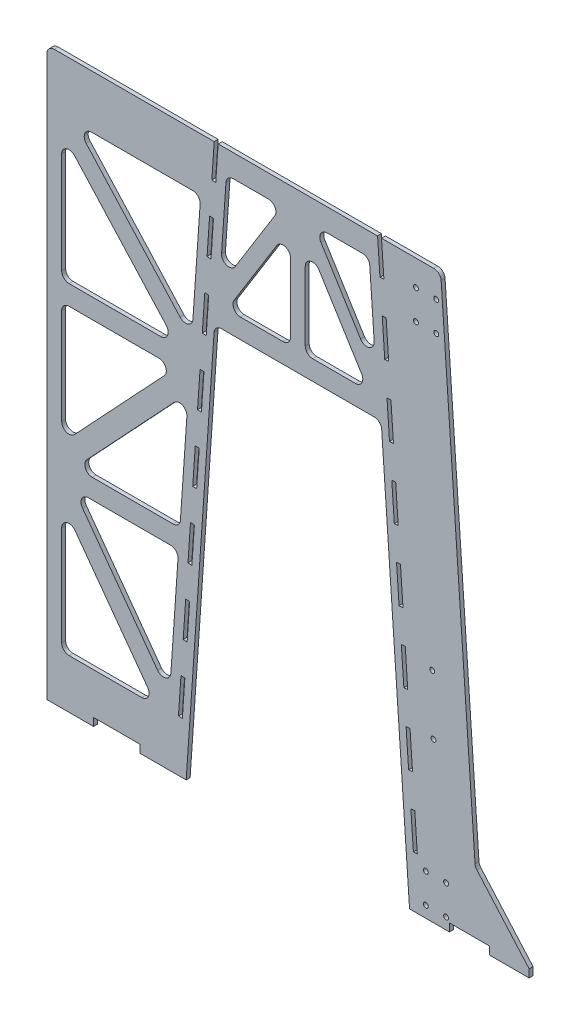
SolidWorks part; units mm, degrees
material "A-Glass Fiber"
ref_plane "Front Plane" through (0, 0, 0) normal (0, 0, 1) x (1, 0, 0)
ref_plane "Top Plane" through (0, 0, 0) normal (0, 1, 0) x (1, 0, 0)
ref_plane "Right Plane" through (0, 0, 0) normal (1, 0, 0) x (0, 0, -1)
sketch "Sketch1" plane through (0, 0, 0) normal (0, 0, 1) x (1, 0, 0)
  line L0 (-288.2759, 0) -> (288.2759, 0) construction
  line L1 (-215.8925, 1463.04) -> (215.8925, 1463.04)
  line L2 (0, 0) -> (0, 1733.4513) construction
  line L3 (19.05, 1104.9) -> (205.1391, 1104.9)
  line L4 (202.3135, 1145.5664) -> (41.4731, 1404.62)
  line L5 (205.1391, 1104.9) -> (19.05, 1404.62) construction
  line L6 (205.1391, 1104.9) -> (184.3133, 1404.62)
  line L7 (182.716, 1104.9) -> (19.05, 1368.5047)
  line L8 (19.05, 1404.62) -> (19.05, 1104.9)
  line L9 (184.3133, 1404.62) -> (19.05, 1404.62)
  line L10 (205.7153, 1463.04) -> (307.3735, 0)
  line L11 (317.5154, 0.5076) -> (215.8925, 1463.04)
  line L12 (317.5154, 0.5076) -> (317.5507, 0)
  line L13 (288.2759, 0) -> (215.0326, 1054.1)
  line L14 (494.0591, 0) -> (391.1675, 0) construction
  line L15 (266.6925, 1463.04) -> (368.5375, 1463.04)
  line L16 (368.5375, 1463.04) -> (457.7693, 178.8376)
  line L81 (215.8925, 1463.04) -> (266.6925, 1463.04)
  line L82 (-215.8925, 1463.04) -> (-647.7182, 1463.04)
  line L88 (317.5507, 0) -> (307.3718, 0)
  line L90 (215.0326, 1054.1) -> (-215.0326, 1054.1)
  line L92 (307.3718, 0) -> (288.2759, 0)
  line L93 (-288.2759, 0) -> (-215.0326, 1054.1)
  line L94 (-307.3735, 0) -> (-288.2759, 0)
  line L97 (-317.5507, 0) -> (-307.3735, 0)
  line L98 (-317.5154, 0.5076) -> (-317.5507, 0)
  line L99 (-317.5154, 0.5076) -> (-215.8925, 1463.04)
  line L100 (-205.7153, 1463.04) -> (-307.3735, 0)
  line L124 (-184.3133, 1404.62) -> (-19.05, 1404.62)
  line L125 (-19.05, 1404.62) -> (-19.05, 1104.9)
  line L126 (-182.716, 1104.9) -> (-19.05, 1368.5047)
  line L127 (-205.1391, 1104.9) -> (-19.05, 1404.62) construction
  line L128 (-202.3135, 1145.5664) -> (-41.4731, 1404.62)
  line L129 (-205.1391, 1104.9) -> (-184.3133, 1404.62)
  line L130 (-19.05, 1104.9) -> (-205.1391, 1104.9)
  line L131 (-317.5507, 0) -> (-647.7182, 0)
  line L132 (-647.7182, 0) -> (-647.7182, 1463.04)
  line L133 (-647.7182, 0) -> (-317.5507, 0)
  line L134 (-308.7262, 127) -> (-647.7182, 127)
  line L135 (-647.7182, 1325.88) -> (-225.423, 1325.88)
  line L136 (317.5507, 0) -> (368.3507, 0)
  line L137 (368.3507, 0) -> (266.6925, 1463.04)
  line L138 (368.3507, 0) -> (317.5507, 0)
  line L139 (-250.8842, 1325.88) -> (-334.1875, 127)
  line L140 (-609.6182, 127) -> (-609.6182, 1325.88)
  line L141 (-306.1844, 530.0133) -> (-609.6182, 530.0133)
  line L142 (-278.1813, 933.0267) -> (-609.6182, 933.0267)
  line L143 (-304.4195, 555.4133) -> (-609.6182, 555.4133)
  line L144 (-307.9493, 504.6133) -> (-609.6182, 504.6133)
  line L145 (-279.9462, 907.6267) -> (-609.6182, 907.6267)
  line L146 (-276.4164, 958.4267) -> (-609.6182, 958.4267)
  line L147 (-334.1875, 127) -> (-609.6182, 504.6133) construction
  line L148 (-609.6182, 555.4133) -> (-279.9462, 907.6267) construction
  line L149 (-276.4164, 958.4267) -> (-609.6182, 1325.88) construction
  line L150 (-331.453, 166.3535) -> (-578.1794, 504.6133)
  line L151 (-574.8276, 555.4133) -> (-282.736, 867.4768)
  line L152 (-273.976, 993.5478) -> (-575.3304, 1325.88)
  line L153 (-365.6263, 127) -> (-609.6182, 461.511)
  line L154 (-609.6182, 592.5827) -> (-314.7368, 907.6267)
  line L155 (-310.7042, 958.4267) -> (-609.6182, 1288.0676)
  line L156 (368.3507, 0) -> (596.9507, 0)
  line L157 (596.9507, 0) -> (596.9507, 20.32)
  line L158 (596.9507, 20.32) -> (347.1719, 304.8)
  point P0 (0, 0)
  point P3 (0, 0)
  point P106 (0, 0)
  point P118 (0, 1054.1)
  dimension "D6" = 25.4
  dimension "D7" = 50.8
  dimension "D8" = 58.42
  dimension "D9" = 19.05
  dimension "D10" = 647.7182
  dimension "D11" = 10.1527
  dimension "D12" = 25.4
  dimension "D13" = 25.4
  dimension "D14" = 25.4
  dimension "D15" = 25.4
  dimension "D16" = 25.4
  dimension "D17" = 25.4
  dimension "D18" = 1463.04
  dimension "D19" = 288.2759
  dimension "D20" = 29.2044
  dimension "D21" = 101.6
  dimension "D22" = 19.05
  dimension "D23" = 19.05
  dimension "D24" = 1054.1
  dimension "D25" = 20.32
  dimension "D37" = 127
  dimension "D38" = 50.8
  dimension "D39" = 25.4
  dimension "D40" = 38.1
  dimension "D41" = 403.0133
  dimension "D42" = 403.0133
  dimension "D43" = 25.4
  dimension "D44" = 25.4
  dimension "D45" = 25.4
  dimension "D46" = 25.4
  dimension "D47" = 279.4
  dimension "D48" = 304.8
  dimension "D49" = 50.8
  dimension "D52" = 137.16
extrude "Boss-Extrude1" add sketch "Sketch1" along normal blind 10.16
fillet "Fillet1" radius 19.05 35 edges at (-215.0326, 1054.1, 5.08) (215.0326, 1054.1, 5.08) (-202.3135, 1145.5664, 5.08) (-19.05, 1104.9, 5.08) (-182.716, 1104.9, 5.08) (-19.05, 1368.5047, 5.08) (-41.4731, 1404.62, 5.08) (-184.3133, 1404.62, 5.08) (-647.7182, 1463.04, 5.08) (-250.8842, 1325.88, 5.08) (-575.3304, 1325.88, 5.08) (-273.976, 993.5478, 5.08) (-609.6182, 958.4267, 5.08) (-609.6182, 1288.0676, 5.08) (-310.7042, 958.4267, 5.08) (-609.6182, 592.5827, 5.08) (-314.7368, 907.6267, 5.08) (-609.6182, 907.6267, 5.08) (-574.8276, 555.4133, 5.08) (-304.4195, 555.4133, 5.08) (-282.736, 867.4768, 5.08) (-307.9493, 504.6133, 5.08) (-331.453, 166.3535, 5.08) (-578.1794, 504.6133, 5.08) (-609.6182, 461.511, 5.08) (-365.6263, 127, 5.08) (-609.6182, 127, 5.08) (19.05, 1104.9, 5.08) (184.3133, 1404.62, 5.08) (41.4731, 1404.62, 5.08) (182.716, 1104.9, 5.08) (19.05, 1368.5047, 5.08) (202.3135, 1145.5664, 5.08) (457.7693, 178.8376, 5.08) (368.5375, 1463.04, 5.08)
sketch "Sketch2" plane through (0, 0, 10.16) normal (0, 0, 1) x (1, 0, 0)
  line L28 (215.8818, 1463.04) -> (205.7153, 1463.04) construction
  line L29 (205.7153, 1463.04) -> (211.9231, 1373.6642) construction
  line L30 (211.9231, 1373.6642) -> (222.0407, 1374.3669) construction
  line L31 (222.0407, 1374.3669) -> (215.8818, 1463.04) construction
  line L32 (217.7192, 1290.2141) -> (224.241, 1196.3181) construction
  line L33 (224.241, 1196.3181) -> (234.3587, 1197.0208) construction
  line L34 (234.3587, 1197.0208) -> (227.8369, 1290.9169) construction
  line L35 (227.8369, 1290.9169) -> (217.7192, 1290.2141) construction
  line L64 (230.039, 1112.8414) -> (236.5589, 1018.9719) construction
  line L65 (236.5589, 1018.9719) -> (246.6766, 1019.6747) construction
  line L66 (246.6766, 1019.6747) -> (240.1567, 1113.5442) construction
  line L67 (240.1567, 1113.5442) -> (230.039, 1112.8414) construction
  line L68 (242.3588, 935.4688) -> (248.8768, 841.6258) construction
  line L69 (248.8768, 841.6258) -> (258.9945, 842.3285) construction
  line L70 (258.9945, 842.3285) -> (252.4764, 936.1715) construction
  line L71 (252.4764, 936.1715) -> (242.3588, 935.4688) construction
  line L72 (254.6785, 758.0961) -> (261.1947, 664.2796) construction
  line L73 (261.1947, 664.2796) -> (271.3124, 664.9824) construction
  line L74 (271.3124, 664.9824) -> (264.7962, 758.7989) construction
  line L75 (264.7962, 758.7989) -> (254.6785, 758.0961) construction
  line L76 (266.9983, 580.7234) -> (273.5126, 486.9335) construction
  line L77 (273.5126, 486.9335) -> (283.6303, 487.6362) construction
  line L78 (283.6303, 487.6362) -> (277.1159, 581.4262) construction
  line L79 (277.1159, 581.4262) -> (266.9983, 580.7234) construction
  line L80 (279.318, 403.3508) -> (285.8305, 309.5874) construction
  line L81 (285.8305, 309.5874) -> (295.9482, 310.2901) construction
  line L82 (295.9482, 310.2901) -> (289.4357, 404.0535) construction
  line L83 (289.4357, 404.0535) -> (279.318, 403.3508) construction
  line L84 (291.6378, 225.9781) -> (298.1484, 132.2412) construction
  line L85 (298.1484, 132.2412) -> (308.2661, 132.944) construction
  line L86 (308.2661, 132.944) -> (301.7555, 226.6808) construction
  line L87 (301.7555, 226.6808) -> (291.6378, 225.9781) construction
  line L116 (215.8818, 1463.04) -> (205.7153, 1463.04)
  line L117 (205.7153, 1463.04) -> (211.9231, 1373.6642)
  line L118 (211.9231, 1373.6642) -> (222.0407, 1374.3669)
  line L119 (222.0407, 1374.3669) -> (215.8818, 1463.04)
  line L120 (217.7192, 1290.2141) -> (224.241, 1196.3181)
  line L121 (224.241, 1196.3181) -> (234.3587, 1197.0208)
  line L122 (234.3587, 1197.0208) -> (227.8369, 1290.9169)
  line L123 (227.8369, 1290.9169) -> (217.7192, 1290.2141)
  line L152 (230.039, 1112.8414) -> (236.5589, 1018.9719)
  line L153 (236.5589, 1018.9719) -> (246.6766, 1019.6747)
  line L154 (246.6766, 1019.6747) -> (240.1567, 1113.5442)
  line L155 (240.1567, 1113.5442) -> (230.039, 1112.8414)
  line L156 (242.3588, 935.4688) -> (248.8768, 841.6258)
  line L157 (248.8768, 841.6258) -> (258.9945, 842.3285)
  line L158 (258.9945, 842.3285) -> (252.4764, 936.1715)
  line L159 (252.4764, 936.1715) -> (242.3588, 935.4688)
  line L160 (254.6785, 758.0961) -> (261.1947, 664.2796)
  line L161 (261.1947, 664.2796) -> (271.3124, 664.9824)
  line L162 (271.3124, 664.9824) -> (264.7962, 758.7989)
  line L163 (264.7962, 758.7989) -> (254.6785, 758.0961)
  line L164 (266.9983, 580.7234) -> (273.5126, 486.9335)
  line L165 (273.5126, 486.9335) -> (283.6303, 487.6362)
  line L166 (283.6303, 487.6362) -> (277.1159, 581.4262)
  line L167 (277.1159, 581.4262) -> (266.9983, 580.7234)
  line L168 (279.318, 403.3508) -> (285.8305, 309.5874)
  line L169 (285.8305, 309.5874) -> (295.9482, 310.2901)
  line L170 (295.9482, 310.2901) -> (289.4357, 404.0535)
  line L171 (289.4357, 404.0535) -> (279.318, 403.3508)
  line L172 (291.6378, 225.9781) -> (298.1484, 132.2412)
  line L173 (298.1484, 132.2412) -> (308.2661, 132.944)
  line L174 (308.2661, 132.944) -> (301.7555, 226.6808)
  line L175 (301.7555, 226.6808) -> (291.6378, 225.9781)
  line L194 (-134.539, 20.32) -> (-288.2759, 20.32) construction
  line L195 (-647.7182, 0) -> (-527.4335, 0)
  line L196 (-647.7182, 0) -> (-647.7182, 20.32)
  line L197 (-647.7182, 20.32) -> (-527.4335, 20.32)
  line L198 (-527.4335, 0) -> (-527.4335, 20.32)
  line L199 (-288.2759, 0) -> (-216.2645, 1036.3705) construction
  line L200 (-527.4335, 0) -> (-407.1487, 0)
  line L201 (-527.4335, 0) -> (-527.4335, 20.32)
  line L202 (-527.4335, 20.32) -> (-407.1487, 20.32)
  line L203 (-407.1487, 0) -> (-407.1487, 20.32)
  line L204 (-407.1487, 0) -> (-286.864, 0)
  line L205 (-407.1487, 0) -> (-407.1487, 20.32)
  line L206 (-407.1487, 20.32) -> (-286.864, 20.32)
  line L207 (-286.864, 0) -> (-286.864, 20.32)
  line L213 (288.2759, 20.32) -> (134.539, 20.32) construction
  line L230 (288.2759, 0) -> (391.1675, 0)
  line L231 (288.2759, 0) -> (288.2759, 20.32)
  line L232 (288.2759, 20.32) -> (391.1675, 20.32)
  line L233 (391.1675, 0) -> (391.1675, 20.32)
  line L235 (391.1675, 0) -> (494.0591, 0)
  line L236 (391.1675, 0) -> (391.1675, 20.32)
  line L237 (391.1675, 20.32) -> (494.0591, 20.32)
  line L238 (494.0591, 0) -> (494.0591, 20.32)
  line L239 (494.0591, 0) -> (596.9507, 0)
  line L240 (494.0591, 0) -> (494.0591, 20.32)
  line L241 (494.0591, 20.32) -> (596.9507, 20.32)
  line L242 (596.9507, 0) -> (596.9507, 20.32)
  line L254 (-205.7153, 1463.04) -> (-215.8818, 1463.04) construction
  line L255 (-215.8818, 1463.04) -> (-222.0407, 1374.3669) construction
  line L256 (-222.0407, 1374.3669) -> (-211.9231, 1373.6642) construction
  line L257 (-211.9231, 1373.6642) -> (-205.7153, 1463.04) construction
  line L258 (-224.241, 1196.3181) -> (-217.7192, 1290.2141) construction
  line L259 (-217.7192, 1290.2141) -> (-227.8369, 1290.9169) construction
  line L260 (-227.8369, 1290.9169) -> (-234.3587, 1197.0208) construction
  line L261 (-234.3587, 1197.0208) -> (-224.241, 1196.3181) construction
  line L262 (-236.5589, 1018.9719) -> (-230.039, 1112.8414) construction
  line L263 (-230.039, 1112.8414) -> (-240.1567, 1113.5442) construction
  line L264 (-240.1567, 1113.5442) -> (-246.6766, 1019.6747) construction
  line L265 (-246.6766, 1019.6747) -> (-236.5589, 1018.9719) construction
  line L266 (-248.8768, 841.6258) -> (-242.3588, 935.4688) construction
  line L267 (-242.3588, 935.4688) -> (-252.4764, 936.1715) construction
  line L268 (-252.4764, 936.1715) -> (-258.9945, 842.3285) construction
  line L269 (-258.9945, 842.3285) -> (-248.8768, 841.6258) construction
  line L270 (-261.1947, 664.2796) -> (-254.6785, 758.0961) construction
  line L271 (-254.6785, 758.0961) -> (-264.7962, 758.7989) construction
  line L272 (-264.7962, 758.7989) -> (-271.3124, 664.9824) construction
  line L273 (-271.3124, 664.9824) -> (-261.1947, 664.2796) construction
  line L274 (-273.5126, 486.9335) -> (-266.9983, 580.7234) construction
  line L275 (-266.9983, 580.7234) -> (-277.1159, 581.4262) construction
  line L276 (-277.1159, 581.4262) -> (-283.6303, 487.6362) construction
  line L277 (-283.6303, 487.6362) -> (-273.5126, 486.9335) construction
  line L278 (-285.8305, 309.5874) -> (-279.318, 403.3508) construction
  line L279 (-279.318, 403.3508) -> (-289.4357, 404.0535) construction
  line L280 (-289.4357, 404.0535) -> (-295.9482, 310.2901) construction
  line L281 (-295.9482, 310.2901) -> (-285.8305, 309.5874) construction
  line L282 (-298.1484, 132.2412) -> (-291.6378, 225.9781) construction
  line L283 (-291.6378, 225.9781) -> (-301.7555, 226.6808) construction
  line L284 (-301.7555, 226.6808) -> (-308.2661, 132.944) construction
  line L285 (-308.2661, 132.944) -> (-298.1484, 132.2412) construction
  line L298 (-205.7153, 1463.04) -> (-215.8818, 1463.04)
  line L299 (-215.8818, 1463.04) -> (-222.0407, 1374.3669)
  line L300 (-222.0407, 1374.3669) -> (-211.9231, 1373.6642)
  line L301 (-211.9231, 1373.6642) -> (-205.7153, 1463.04)
  line L302 (-224.241, 1196.3181) -> (-217.7192, 1290.2141)
  line L303 (-217.7192, 1290.2141) -> (-227.8369, 1290.9169)
  line L304 (-227.8369, 1290.9169) -> (-234.3587, 1197.0208)
  line L305 (-234.3587, 1197.0208) -> (-224.241, 1196.3181)
  line L306 (-236.5589, 1018.9719) -> (-230.039, 1112.8414)
  line L307 (-230.039, 1112.8414) -> (-240.1567, 1113.5442)
  line L308 (-240.1567, 1113.5442) -> (-246.6766, 1019.6747)
  line L309 (-246.6766, 1019.6747) -> (-236.5589, 1018.9719)
  line L310 (-248.8768, 841.6258) -> (-242.3588, 935.4688)
  line L311 (-242.3588, 935.4688) -> (-252.4764, 936.1715)
  line L312 (-252.4764, 936.1715) -> (-258.9945, 842.3285)
  line L313 (-258.9945, 842.3285) -> (-248.8768, 841.6258)
  line L314 (-261.1947, 664.2796) -> (-254.6785, 758.0961)
  line L315 (-254.6785, 758.0961) -> (-264.7962, 758.7989)
  line L316 (-264.7962, 758.7989) -> (-271.3124, 664.9824)
  line L317 (-271.3124, 664.9824) -> (-261.1947, 664.2796)
  line L318 (-273.5126, 486.9335) -> (-266.9983, 580.7234)
  line L319 (-266.9983, 580.7234) -> (-277.1159, 581.4262)
  line L320 (-277.1159, 581.4262) -> (-283.6303, 487.6362)
  line L321 (-283.6303, 487.6362) -> (-273.5126, 486.9335)
  line L322 (-285.8305, 309.5874) -> (-279.318, 403.3508)
  line L323 (-279.318, 403.3508) -> (-289.4357, 404.0535)
  line L324 (-289.4357, 404.0535) -> (-295.9482, 310.2901)
  line L325 (-295.9482, 310.2901) -> (-285.8305, 309.5874)
  line L326 (-298.1484, 132.2412) -> (-291.6378, 225.9781)
  line L327 (-291.6378, 225.9781) -> (-301.7555, 226.6808)
  line L328 (-301.7555, 226.6808) -> (-308.2661, 132.944)
  line L329 (-308.2661, 132.944) -> (-298.1484, 132.2412)
extrude "Cut-Extrude1" cut sketch "Sketch2" against normal blind 12.7 contours L200 L203 L202 L198 | L235 L238 L237 L233 | L118 L119 L116 L117 | L122 L123 L120 L121 | L154 L155 L152 L153 | L158 L159 L156 L157 | L162 L163 L160 L161 | L166 L167 L164 L165 | L170 L171 L168 L169 | L174 L175 L172 L173 | L328 L329 L326 L327 | L324 L325 L322 L323 | L320 L321 L318 L319 | L316 L317 L314 L315 | L312 L313 L310 L311 | L308 L309 L306 L307 | L304 L305 L302 L303 | L300 L301 L298 L299
sketch "Sketch4" [suppressed] plane through (0, 0, 10.16) normal (0, 0, 1) x (1, 0, 0)
  line L0 (596.9507, 0) -> (494.0591, 0) construction
  line L1 (596.9507, 0) -> (596.9507, 20.32) construction
  line L2 (596.9507, 0) -> (494.0591, 0)
  line L3 (596.9507, 0) -> (596.9507, 20.32)
  line L4 (337.4418, 445.6368) -> (336.7375, 455.7724)
  line L5 (337.4418, 445.6368) -> (286.7919, 442.1174)
  line L6 (336.7375, 455.7724) -> (286.0876, 452.253)
  line L7 (286.7919, 442.1174) -> (286.0876, 452.253)
  line L8 (388.0923, 449.1521) -> (387.388, 459.2876)
  line L9 (388.0923, 449.1521) -> (438.7422, 452.6714)
  line L10 (387.388, 459.2876) -> (438.0379, 462.807)
  line L11 (438.7422, 452.6714) -> (438.0379, 462.807)
  line L12 (369.7694, 1445.3105) -> (457.3235, 185.2533) construction
  point P2 (596.9507, 0)
sketch "Sketch6" plane through (0, 0, 10.16) normal (0, 0, 1) x (1, 0, 0)
  line L0 (0, 1463.04) -> (0, 0) construction
  line L1 (205.7153, 1463.04) -> (-205.7153, 1463.04) construction
  line L2 (0, 1463.04) -> (515.0924, 1463.04) construction
  line L3 (350.7652, 1463.04) -> (215.8818, 1463.04) construction
  line L4 (304.8, 1320.8) -> (357.1875, 1320.8) construction
  line L5 (304.8, 1320.8) -> (304.8, 1397) construction
  line L6 (304.8, 1397) -> (357.1875, 1397) construction
  line L7 (357.1875, 1320.8) -> (357.1875, 1397) construction
  line L8 (304.8, 1320.8) -> (357.1875, 1397) construction
  line L9 (304.8, 1397) -> (357.1875, 1320.8) construction
  line L10 (330.2, 29.21) -> (382.5875, 29.21) construction
  line L11 (330.2, 29.21) -> (330.2, 105.41) construction
  line L12 (330.2, 105.41) -> (382.5875, 105.41) construction
  line L13 (382.5875, 29.21) -> (382.5875, 105.41) construction
  line L14 (330.2, 29.21) -> (382.5875, 105.41) construction
  line L15 (330.2, 105.41) -> (382.5875, 29.21) construction
  line L17 (391.1675, 0) -> (288.2759, 0) construction
  line L18 (330.9937, 1320.8) -> (356.3938, 105.41) construction
  circle A0 centre (357.1875, 1397) radius 6.35
  circle A1 centre (357.1875, 1320.8) radius 6.35
  circle A2 centre (304.8, 1320.8) radius 6.35
  circle A3 centre (304.8, 1397) radius 6.35
  circle A4 centre (382.5875, 105.41) radius 6.35
  circle A5 centre (382.5875, 29.21) radius 6.35
  circle A6 centre (330.2, 29.21) radius 6.35
  circle A7 centre (330.2, 105.41) radius 6.35
  circle A8 centre (350.0238, 410.21) radius 6.35
  circle A9 centre (346.8389, 562.61) radius 6.35
  point P5 (356.3937, 67.31)
  point P7 (330.9937, 1358.9)
  dimension "D6" = 12.7
  dimension "D7" = 12.7
  dimension "D8" = 12.7
  dimension "D9" = 12.7
  dimension "D10" = 12.7
  dimension "D11" = 12.7
  dimension "D16" = 152.4
  dimension "D1" = 52.3875
  dimension "D2" = 66.04
  dimension "D3" = 52.3875
  dimension "D4" = 76.2
  dimension "D5" = 304.8
  dimension "D12" = 330.2
  dimension "D13" = 29.21
  dimension "D14" = 76.2
  dimension "D15" = 304.8
extrude "Cut-Extrude2" cut sketch "Sketch6" against normal blind 10.16
